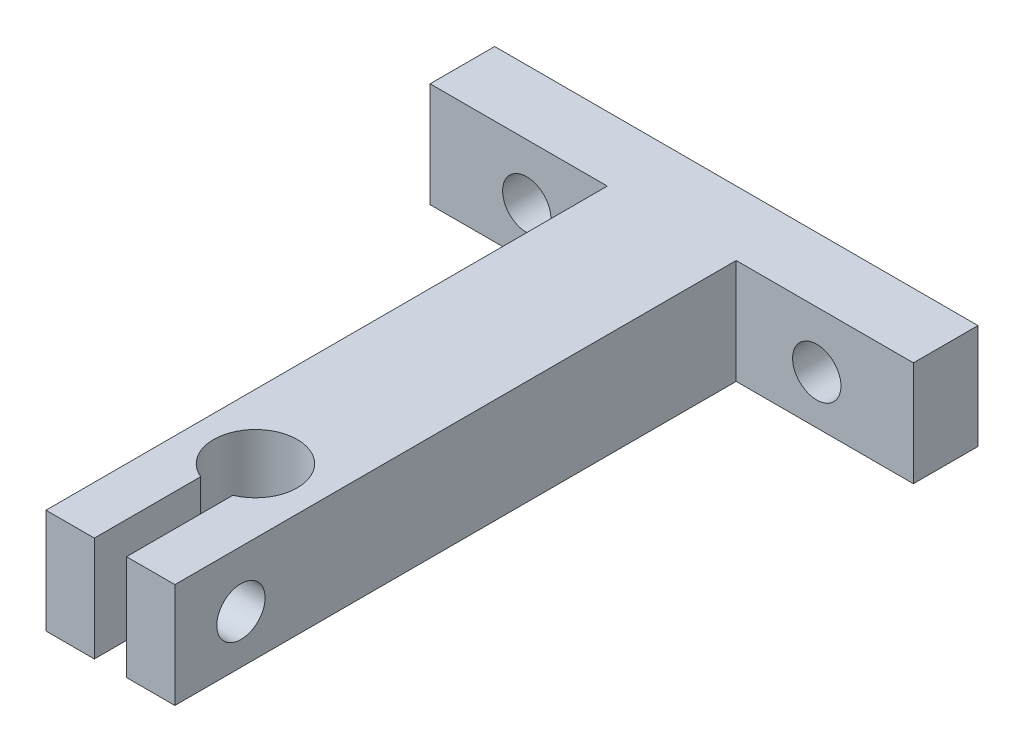
SolidWorks part; units mm, degrees
ref_plane "Front Plane" through (0, 0, 0) normal (0, 0, 1) x (1, 0, 0)
ref_plane "Top Plane" through (0, 0, 0) normal (0, 1, 0) x (1, 0, 0)
ref_plane "Right Plane" through (0, 0, 0) normal (1, 0, 0) x (0, 0, -1)
sketch "Sketch1" plane through (0, 0, 0) normal (0, 1, 0) x (1, 0, 0)
  line L0 (0, -21.725) -> (0, 21.725) construction
  line L1 (-15, 2.0042) -> (15, 2.0042)
  line L2 (-15, 2.0042) -> (-15, -2.0042)
  line L3 (-15, -2.0042) -> (15, -2.0042)
  line L4 (15, 2.0042) -> (15, -2.0042)
  line L5 (-15, 2.0042) -> (15, -2.0042) construction
  line L6 (-15, -2.0042) -> (15, 2.0042) construction
  line L7 (4, -2.0042) -> (-4, -2.0042)
  line L8 (4, -2.0042) -> (4, -36.8458)
  line L9 (4, -36.8458) -> (-4, -36.8458)
  line L10 (-4, -2.0042) -> (-4, -36.8458)
  line L12 (1, -36.8458) -> (-1, -36.8458)
  line L13 (1, -36.8458) -> (1, -30.2458)
  line L14 (1, -30.2458) -> (-1, -30.2458)
  line L15 (-1, -36.8458) -> (-1, -30.2458)
  circle A0 centre (0, -27.8458) radius 2.6
  point P0 (0, 0)
  point P10 (0, -36.8458)
  point P19 (0, -30.2458)
  dimension "D3" = 5.2
  dimension "D1" = 30
  dimension "D2" = 8
  dimension "D4" = 29.85
  dimension "D5" = 9
  dimension "D6" = 2
extrude "Boss-Extrude1" add sketch "Sketch1" along normal blind 7 contours A0 L13 L9 L8 L3 L10 L15 | L4 L1 L2 L3
sketch "Sketch2" plane through (4, 0, 0) normal (1, 0, 0) x (0, 0, -1)
  line L0 (-36.8458, 3.5) -> (-27.6933, 3.5) construction
  line L1 (-36.8458, 7) -> (-36.8458, 0) construction
  line L2 (-30.2458, 7) -> (-30.2458, 0) construction
  circle A0 centre (-32.7458, 3.5) radius 1.5
  dimension "D1" = 3
  dimension "D2" = 2.5
extrude "Cut-Extrude1" cut sketch "Sketch2" against normal through all
sketch "Sketch3" plane through (0, 0, 2.0042) normal (0, 0, 1) x (1, 0, 0)
  line L0 (15, 3.5) -> (7.0219, 3.5) construction
  line L1 (15, 7) -> (15, 0) construction
  line L2 (4, 7) -> (4, 0) construction
  line L3 (0, -21.725) -> (0, 21.725) construction
  circle A0 centre (9, 3.5) radius 1.5
  circle A1 centre (-9, 3.5) radius 1.5
  dimension "D1" = 3
  dimension "D2" = 5
extrude "Cut-Extrude2" cut sketch "Sketch3" against normal blind 5
chamfer "Chamfer1" distance 0.5 angle 50 12 edges at (1, 0, 33.5458) (2.5, 0, 36.8458) (4, 0, 19.425) (9.5, 0, 2.0042) (15, 0, 0) (0, 0, -2.0042) (-15, 0, 0) (-9.5, 0, 2.0042) (-4, 0, 19.425) (-2.5, 0, 36.8458) (-1, 0, 33.5458) (0, 0, 25.2458)
